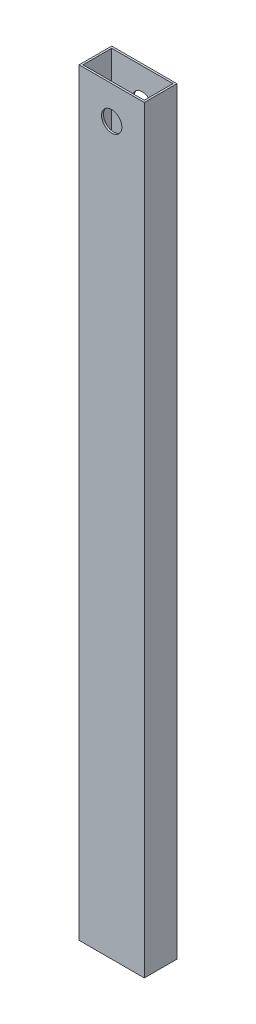
SolidWorks part; units mm, degrees
ref_plane "Front Plane" through (0, 0, 0) normal (0, 0, 1) x (1, 0, 0)
ref_plane "Top Plane" through (0, 0, 0) normal (0, 1, 0) x (1, 0, 0)
ref_plane "Right Plane" through (0, 0, 0) normal (1, 0, 0) x (0, 0, -1)
sketch "Sketch1" plane through (0, 0, 0) normal (0, 1, 0) x (1, 0, 0)
  line L1 (-26.2965, 4.0341) -> (24.5035, 4.0341)
  line L2 (-26.2965, 4.0341) -> (-26.2965, -21.3659)
  line L3 (-26.2965, -21.3659) -> (24.5035, -21.3659)
  line L4 (24.5035, 4.0341) -> (24.5035, -21.3659)
  line L5 (-24.7725, 2.5101) -> (22.9795, 2.5101)
  line L6 (-24.7725, 2.5101) -> (-24.7725, -19.8419)
  line L7 (-24.7725, -19.8419) -> (22.9795, -19.8419)
  line L8 (22.9795, 2.5101) -> (22.9795, -19.8419)
  dimension "D1" = 50.8
  dimension "D2" = 25.4
  dimension "D3" = 1.524
  dimension "D4" = 1.524
  dimension "D5" = 1.524
  dimension "D6" = 1.524
extrude "Boss-Extrude2" add sketch "Sketch1" along normal blind 590.55
sketch "Sketch2" plane through (0, 0, 21.3659) normal (0, 0, 1) x (1, 0, 0)
  line L0 (24.5035, 590.55) -> (24.5035, 0) construction
  line L1 (-26.2965, 590.55) -> (24.5035, 590.55) construction
  circle A0 centre (-0.8965, 565.15) radius 7.9375
  dimension "D1" = 15.875
  dimension "D2" = 25.4
  dimension "D3" = 25.4
extrude "Cut-Extrude1" cut sketch "Sketch2" against normal through all
